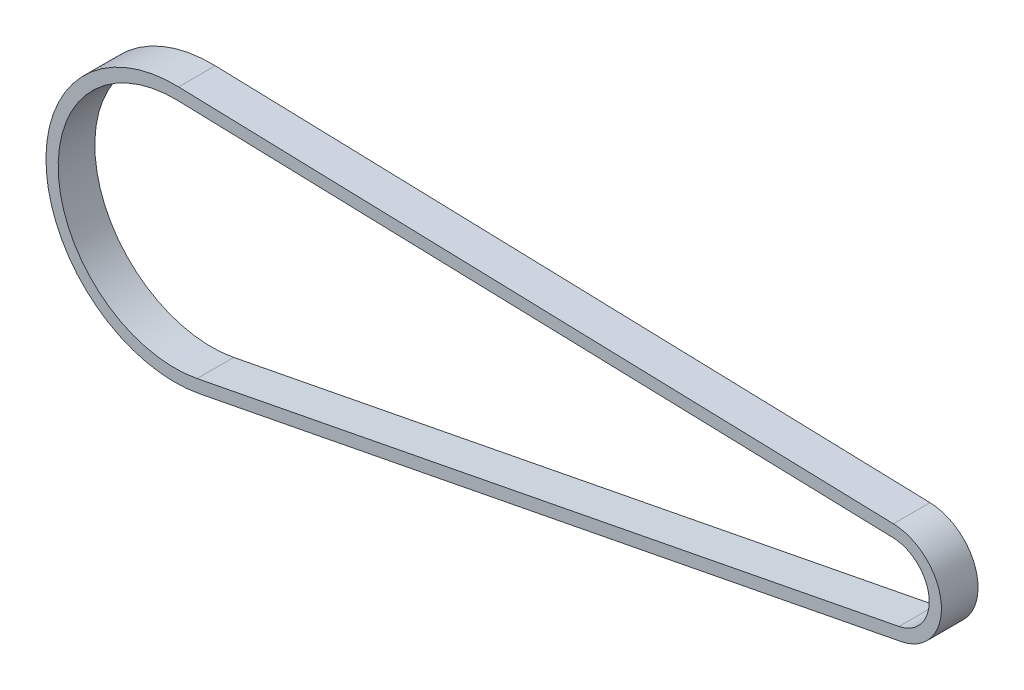
SolidWorks part; units mm, degrees
ref_plane "Front Plane" through (0, 0, 0) normal (0, 0, 1) x (1, 0, 0)
ref_plane "Top Plane" through (0, 0, 0) normal (0, 1, 0) x (1, 0, 0)
ref_plane "Right Plane" through (0, 0, 0) normal (1, 0, 0) x (0, 0, -1)
sketch "Sketch1" plane through (0, 0, 0) normal (0, 0, 1) x (1, 0, 0)
  line L0 (0.5604, 19.1018) -> (117.6408, 15.667)
  line L1 (118.626, 3.5616) -> (3.6417, -18.7598)
  line L2 (0.619, 21.1009) -> (117.6995, 17.6661)
  line L3 (119.0071, 1.5982) -> (4.0229, -20.7231)
  arc A0 (0.5604, 19.1018) -> (3.6417, -18.7598) centre (0, 0) ccw
  arc A1 (118.626, 3.5616) -> (117.6408, 15.667) centre (117.4616, 9.5596) ccw
  arc A2 (119.0071, 1.5982) -> (117.6995, 17.6661) centre (117.4616, 9.5596) ccw
  arc A3 (0.619, 21.1009) -> (4.0229, -20.7231) centre (0, 0) ccw
  dimension "D1" = 117.85
  dimension "D2" = 38.22
  dimension "D3" = 12.22
  dimension "D4" = 2
extrude "Boss-Extrude1" add sketch "Sketch1" along normal blind 6
